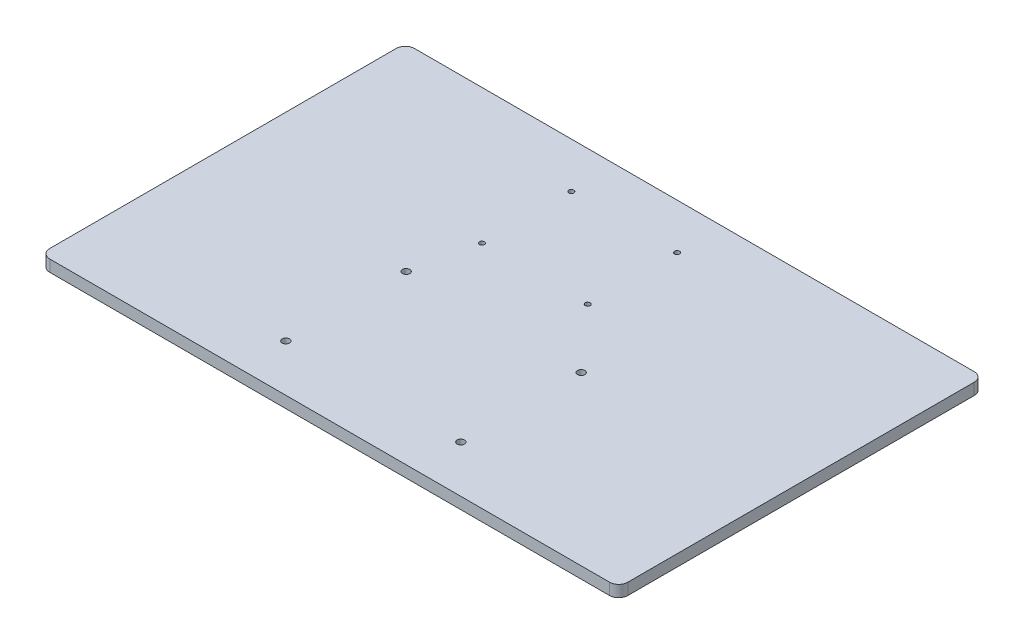
SolidWorks part; units mm, degrees
material "Pine"
ref_plane "Front Plane" through (0, 0, 0) normal (0, 0, 1) x (1, 0, 0)
ref_plane "Top Plane" through (0, 0, 0) normal (0, 1, 0) x (1, 0, 0)
ref_plane "Right Plane" through (0, 0, 0) normal (1, 0, 0) x (0, 0, -1)
sketch "Sketch1" plane through (0, 0, 0) normal (0, 1, 0) x (1, 0, 0)
  line L1 (-158.5, 100) -> (158.5, 100)
  line L2 (-158.5, 100) -> (-158.5, -100)
  line L3 (-158.5, -100) -> (158.5, -100)
  line L4 (158.5, 100) -> (158.5, -100)
  line L5 (-158.5, 100) -> (158.5, -100) construction
  line L6 (-158.5, -100) -> (158.5, 100) construction
  point P0 (0, 0)
  dimension "D1" = 317
  dimension "D2" = 200
extrude "Boss-Extrude1" add sketch "Sketch1" against normal blind 6.35
fillet "Fillet1" radius 5
extrude "Cut-Extrude1" cut sketch "Sketch2" against normal blind 10
sketch "Sketch2" plane through (93.325, 0, -211.68) normal (0, 1, 0) x (0, 0, -1)
  circle A4 centre (-219.881, 47.1776) radius 2
  circle A5 centre (-285.881, 47.1776) radius 2
  circle A6 centre (-219.881, 143.1776) radius 2
  circle A7 centre (-285.881, 143.1776) radius 2
  circle A12 centre (-136.6482, 77.8397) radius 1.375
  circle A13 centre (-185.6482, 77.8397) radius 1.375
  circle A14 centre (-185.6482, 135.8397) radius 1.375
  circle A15 centre (-136.6482, 135.8397) radius 1.375
